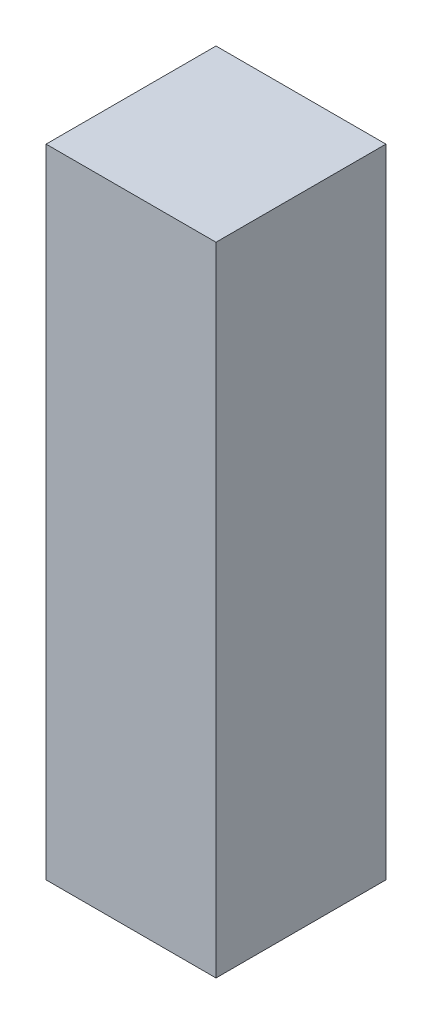
SolidWorks part; units mm, degrees
ref_plane "Front Plane" through (0, 0, 0) normal (0, 0, 1) x (1, 0, 0)
ref_plane "Top Plane" through (0, 0, 0) normal (0, 1, 0) x (1, 0, 0)
ref_plane "Right Plane" through (0, 0, 0) normal (1, 0, 0) x (0, 0, -1)
sketch "Sketch2" plane through (0, 0, 0) normal (0, 1, 0) x (1, 0, 0)
  line L1 (0, 0.8) -> (0.8, 0.8)
  line L2 (0, 0.8) -> (0, 0)
  line L3 (0, 0) -> (0.8, 0)
  line L4 (0.8, 0.8) -> (0.8, 0)
  point P4 (0, 0)
  dimension "D1" = 0.8
  dimension "D2" = 0.8
extrude "Boss-Extrude1" add sketch "Sketch2" along normal blind 3
